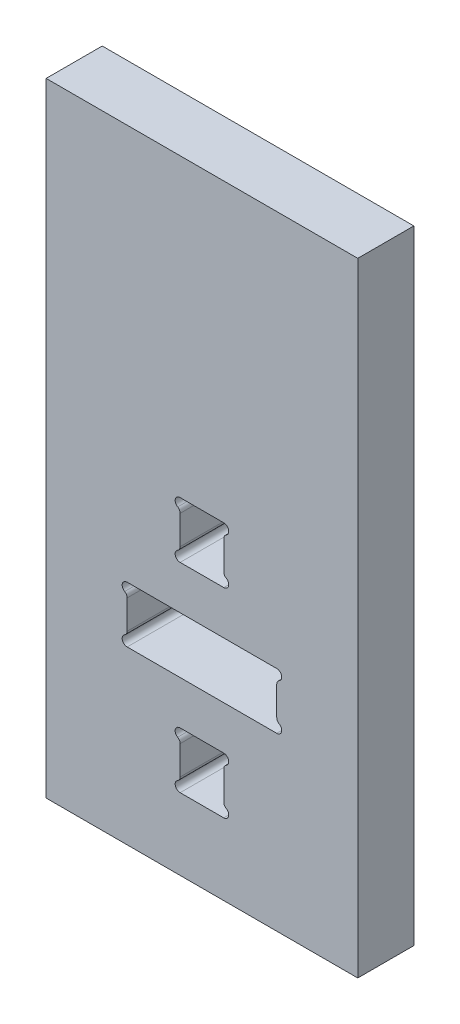
SolidWorks part; units mm, degrees
ref_plane "Front Plane" through (0, 0, 0) normal (0, 0, 1) x (1, 0, 0)
ref_plane "Top Plane" through (0, 0, 0) normal (0, 1, 0) x (1, 0, 0)
ref_plane "Right Plane" through (0, 0, 0) normal (1, 0, 0) x (0, 0, -1)
sketch "Sketch1" plane through (0, 0, 0) normal (0, 0, 1) x (1, 0, 0)
  line L1 (0, 0) -> (25, 0)
  line L2 (0, 0) -> (0, 50)
  line L3 (0, 50) -> (25, 50)
  line L4 (25, 0) -> (25, 50)
  dimension "D1" = 50
  dimension "D2" = 25
extrude "Boss-Extrude1" add sketch "Sketch1" along normal blind 4.5
sketch "Sketch2" plane through (0, 0, 4.5) normal (0, 0, 1) x (1, 0, 0)
  line L0 (12.5, 50) -> (12.5, 0) construction
  line L1 (25, 50) -> (0, 50) construction
  line L2 (0, 0) -> (25, 0) construction
  line L3 (12.5, 10.25) -> (14.25, 10.25)
  line L4 (14.25, 9.1572) -> (14.25, 8)
  line L5 (12.5, 8) -> (26.1621, 8) construction
  line L6 (14.25, 6.8428) -> (14.25, 8)
  line L7 (12.5, 5.75) -> (14.25, 5.75)
  line L8 (12.5, 5.75) -> (10.75, 5.75)
  line L9 (10.75, 6.8428) -> (10.75, 8)
  line L10 (10.75, 9.1572) -> (10.75, 8)
  line L11 (12.5, 10.25) -> (10.75, 10.25)
  arc A0 (14.25, 10.25) -> (14.45, 9.5036) centre (14.25, 9.85) cw
  arc A1 (14.45, 9.5036) -> (14.25, 9.1572) centre (14.65, 9.1572) ccw
  arc A2 (14.45, 6.4964) -> (14.25, 6.8428) centre (14.65, 6.8428) cw
  arc A3 (14.25, 5.75) -> (14.45, 6.4964) centre (14.25, 6.15) ccw
  arc A4 (10.75, 5.75) -> (10.55, 6.4964) centre (10.75, 6.15) cw
  arc A5 (10.55, 6.4964) -> (10.75, 6.8428) centre (10.35, 6.8428) ccw
  arc A6 (10.55, 9.5036) -> (10.75, 9.1572) centre (10.35, 9.1572) cw
  arc A7 (10.75, 10.25) -> (10.55, 9.5036) centre (10.75, 9.85) ccw
  dimension "D1" = 0.4
  dimension "D2" = 4.5
  dimension "D3" = 3.5
  dimension "D4" = 8
extrude "Cut-Extrude1" cut sketch "Sketch2" against normal up to next (4.5 mm away)
pattern_linear "LPattern1" count 2 spacing 16 along (0, 1, 0) of "Cut-Extrude1"
sketch "Sketch3" plane through (0, 0, 4.5) normal (0, 0, 1) x (1, 0, 0)
  line L0 (12.5, 50) -> (12.5, 0) construction
  line L1 (25, 50) -> (0, 50) construction
  line L2 (0, 0) -> (25, 0) construction
  line L3 (6.5, 18.25) -> (18.5, 18.25)
  line L4 (18.5, 17.1572) -> (18.5, 14.8428)
  line L5 (18.5, 16) -> (12.5, 16) construction
  line L6 (6.5, 13.75) -> (18.5, 13.75)
  line L7 (6.5, 17.1572) -> (6.5, 14.8428)
  arc A0 (18.5, 18.25) -> (18.7, 17.5036) centre (18.5, 17.85) cw
  arc A1 (18.7, 17.5036) -> (18.5, 17.1572) centre (18.9, 17.1572) ccw
  arc A2 (18.7, 14.4964) -> (18.5, 14.8428) centre (18.9, 14.8428) cw
  arc A3 (18.5, 13.75) -> (18.7, 14.4964) centre (18.5, 14.15) ccw
  arc A4 (6.5, 13.75) -> (6.3, 14.4964) centre (6.5, 14.15) cw
  arc A5 (6.3, 14.4964) -> (6.5, 14.8428) centre (6.1, 14.8428) ccw
  arc A6 (6.3, 17.5036) -> (6.5, 17.1572) centre (6.1, 17.1572) cw
  arc A7 (6.5, 18.25) -> (6.3, 17.5036) centre (6.5, 17.85) ccw
  point P19 (12.5, 18.25)
  point P30 (12.5, 13.75)
  dimension "D1" = 0.4
  dimension "D2" = 4.5
  dimension "D3" = 12
  dimension "D4" = 16
extrude "Cut-Extrude2" cut sketch "Sketch3" against normal up to next
